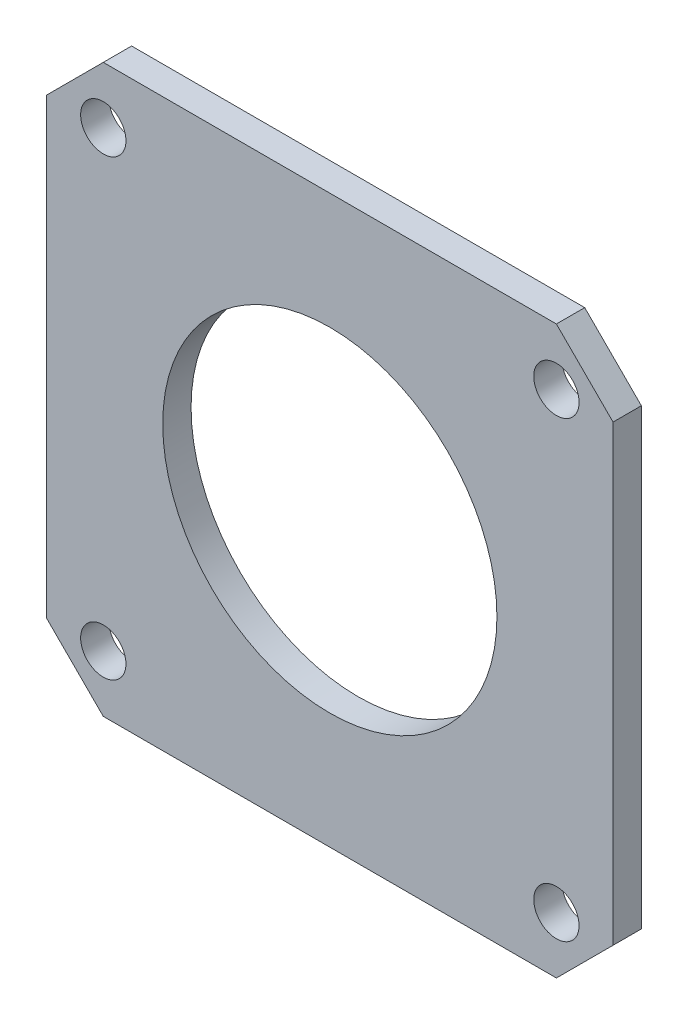
SolidWorks part; units mm, degrees
ref_plane "Front Plane" through (0, 0, 0) normal (0, 0, 1) x (1, 0, 0)
ref_plane "Top Plane" through (0, 0, 0) normal (0, 1, 0) x (1, 0, 0)
ref_plane "Right Plane" through (0, 0, 0) normal (1, 0, 0) x (0, 0, -1)
sketch "Sketch2" plane through (0, 0, 0) normal (0, 0, 1) x (1, 0, 0)
  line L8 (-40, 50) -> (-50, 40)
  line L9 (-40, 50) -> (40, 50)
  line L10 (-50, 40) -> (-50, -40)
  line L11 (-40, -50) -> (40, -50)
  line L12 (50, 40) -> (50, -40)
  line L13 (-50, 50) -> (50, -50) construction
  line L14 (-50, -50) -> (50, 50) construction
  line L15 (40, 50) -> (50, 40)
  line L16 (50, -40) -> (40, -50)
  line L17 (-50, -40) -> (-40, -50)
  circle A0 centre (0, 0) radius 29.5
  circle A1 centre (-40, 40) radius 4
  circle A2 centre (40, 40) radius 4
  circle A3 centre (40, -40) radius 4
  circle A4 centre (-40, -40) radius 4
  dimension "D1" = 59
  dimension "D3" = 8
  dimension "D2" = 100
  dimension "D4" = 10
  dimension "D9" = 10
  dimension "D10" = 10
  dimension "D11" = 10
  dimension "D12" = 80
extrude "Boss-Extrude2" add sketch "Sketch2" along normal blind 5
